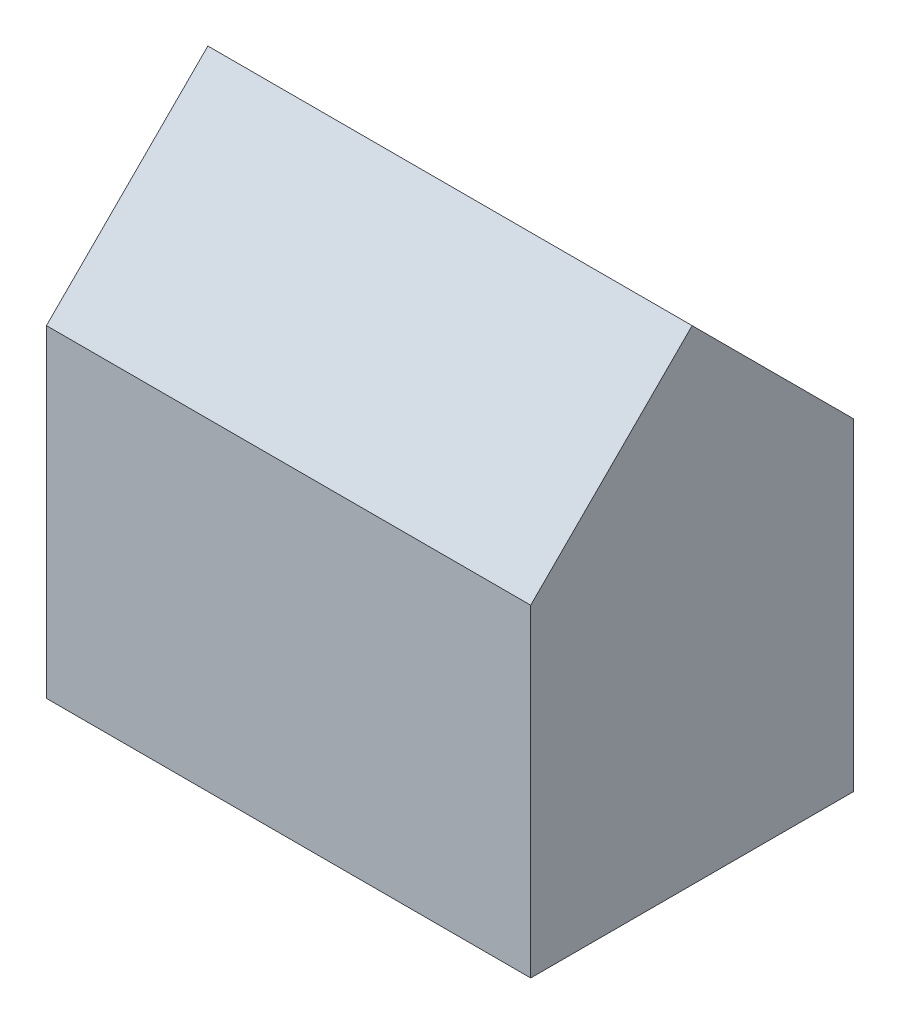
SolidWorks part; units mm, degrees
ref_plane "Front Plane" through (0, 0, 0) normal (0, 0, 1) x (1, 0, 0)
ref_plane "Top Plane" through (0, 0, 0) normal (0, 1, 0) x (1, 0, 0)
ref_plane "Right Plane" through (0, 0, 0) normal (1, 0, 0) x (0, 0, -1)
sketch "Sketch1" plane through (0, 0, 0) normal (0, 1, 0) x (1, 0, 0)
  line L1 (0, 0) -> (15, 0)
  line L2 (0, 0) -> (0, 10)
  line L3 (0, 10) -> (15, 10)
  line L4 (15, 0) -> (15, 10)
  line L5 (2, 2) -> (13, 2)
  line L6 (2, 2) -> (2, 8)
  line L7 (2, 8) -> (13, 8)
  line L8 (13, 2) -> (13, 8)
  dimension "D1" = 15
  dimension "D2" = 10
  dimension "D3" = 2
  dimension "D4" = 2
  dimension "D5" = 2
  dimension "D6" = 2
extrude "Boss-Extrude1" add sketch "Sketch1" along normal blind 10
sketch "Sketch2" plane through (15, 0, 0) normal (1, 0, 0) x (0, 0, -1)
  line L0 (0, 10) -> (5, 15)
  line L1 (5, 15) -> (10, 10)
  line L6 (0, 0) -> (10, 0)
  line L7 (10, 0) -> (10, 10)
  line L8 (10, 10) -> (0, 10)
  line L9 (0, 10) -> (0, 0)
  line L12 (10, 10) -> (0, 10)
  dimension "D1" = 5
  dimension "D2" = 0
extrude "Boss-Extrude2" add sketch "Sketch2" against normal blind 15
